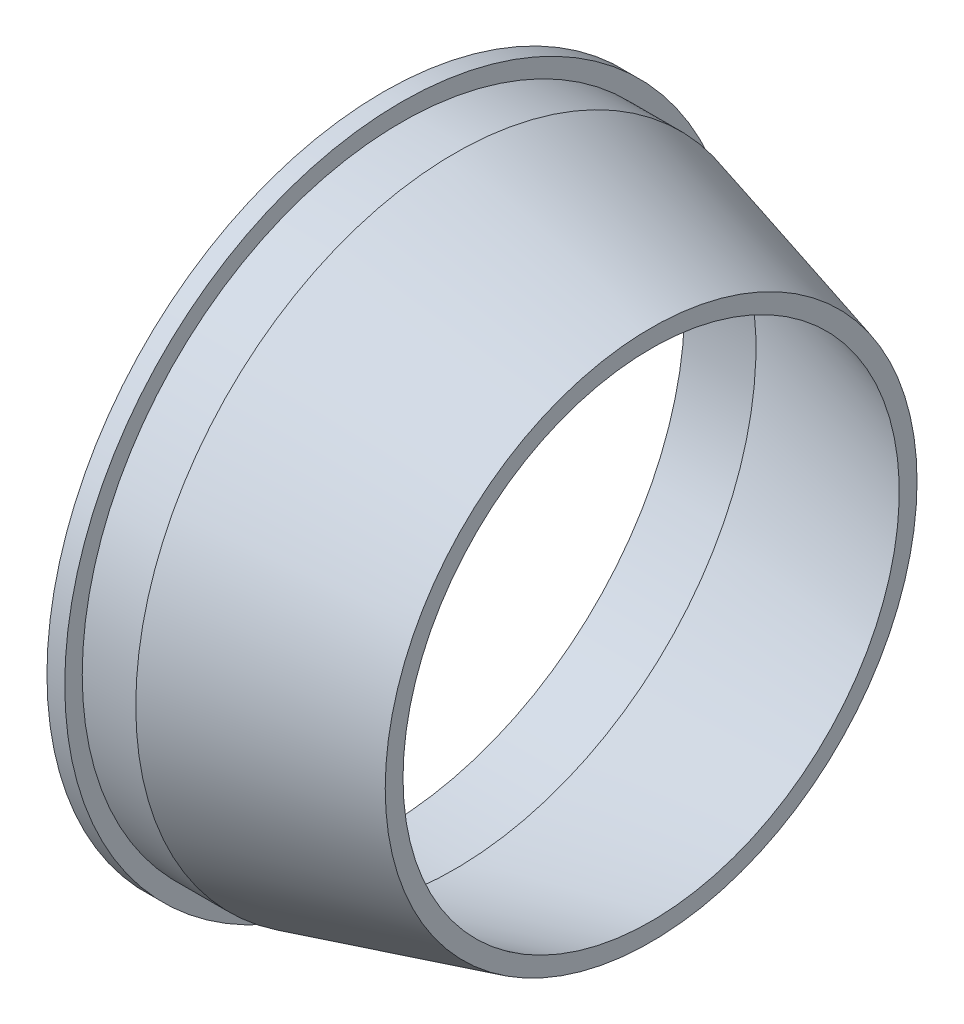
SolidWorks part; units mm, degrees
ref_plane "Front Plane" through (0, 0, 0) normal (0, 0, 1) x (1, 0, 0)
ref_plane "Top Plane" through (0, 0, 0) normal (0, 1, 0) x (1, 0, 0)
ref_plane "Right Plane" through (0, 0, 0) normal (1, 0, 0) x (0, 0, -1)
sketch "Sketch2" plane through (0, 0, 0) normal (0, 0, 1) x (1, 0, 0)
  line L0 (0, 0) -> (63.8395, 0) construction
  line L1 (0, 0) -> (0, 45) construction
  line L2 (0, 45) -> (0, 50.2711)
  line L3 (0, 50.2711) -> (2.66, 50.2711)
  line L4 (2.66, 50.2711) -> (2.66, 47.66)
  line L5 (2.66, 47.66) -> (10.66, 47.66)
  line L6 (0, 45) -> (10.66, 45)
  line L7 (10.66, 45) -> (40, 37.071)
  line L8 (10.66, 47.66) -> (40, 39.731)
  line L9 (40, 39.731) -> (40, 37.071)
  dimension "D1" = 45
  dimension "D2" = 2.66
  dimension "D3" = 2.66
  dimension "D4" = 8
  dimension "D5" = 10.66
  dimension "D6" = 40
revolve "Revolve1" add sketch "Sketch2" angle 360 about L0
sketch "Sketch3" plane through (0, 0, 0) normal (-1, 0, 0) x (0, 0, 1)
  circle A0 centre (0, 0) radius 46.5 construction
  circle A1 centre (0, 0) radius 45 construction
  circle A2 centre (0, -46.5) radius 1
  circle A3 centre (-46.5, 0) radius 1
  circle A4 centre (0, 46.5) radius 1
  circle A5 centre (46.5, 0) radius 1
  point P16 (0, 0)
  dimension "D1" = 1.5
  dimension "D2" = 2
  dimension "D3" = 4
extrude "Cut-Extrude1" cut sketch "Sketch3" against normal blind 10
